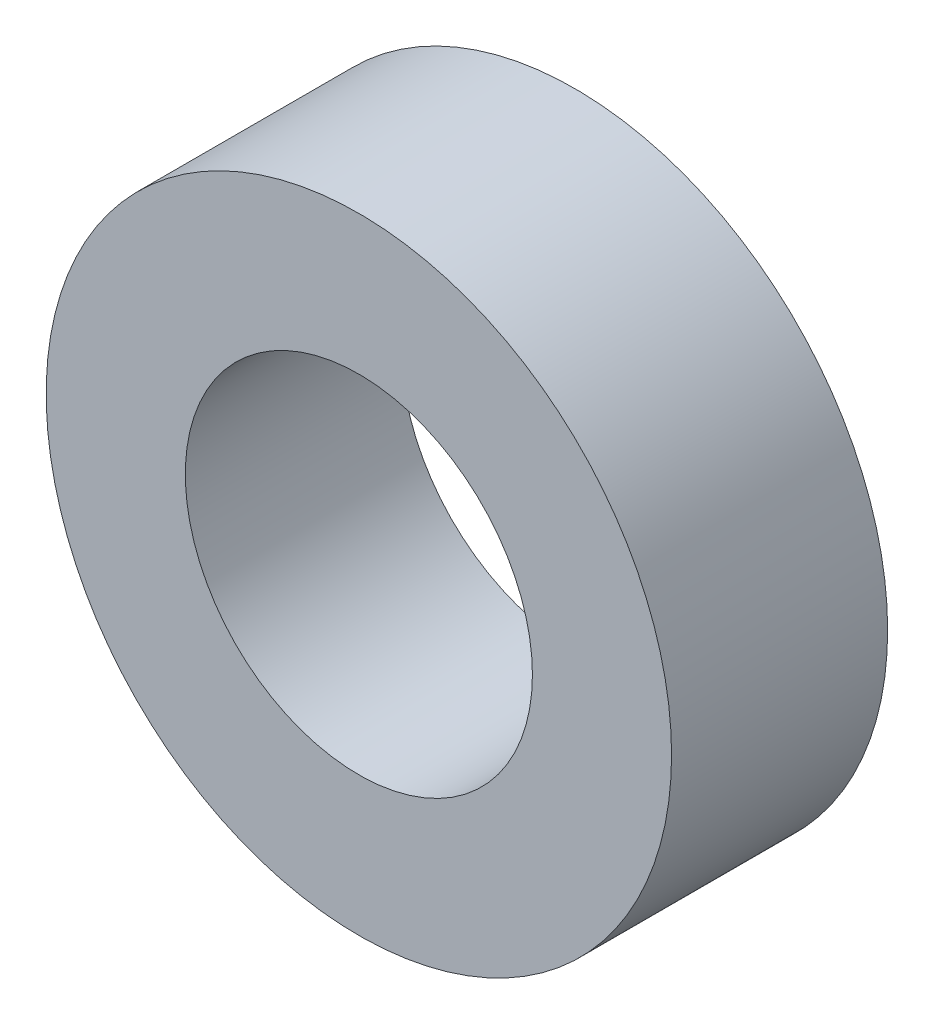
SolidWorks part; units mm, degrees
ref_plane "Front Plane" through (0, 0, 0) normal (0, 0, 1) x (1, 0, 0)
ref_plane "Top Plane" through (0, 0, 0) normal (0, 1, 0) x (1, 0, 0)
ref_plane "Right Plane" through (0, 0, 0) normal (1, 0, 0) x (0, 0, -1)
sketch "Sketch1" plane through (0, 0, 0) normal (0, 0, 1) x (1, 0, 0)
  circle A0 centre (11.2986, 11.8725) radius 5.55
  circle A1 centre (11.2986, 11.8725) radius 10
extrude "Boss-Extrude1" add sketch "Sketch1" along normal blind 6.91
